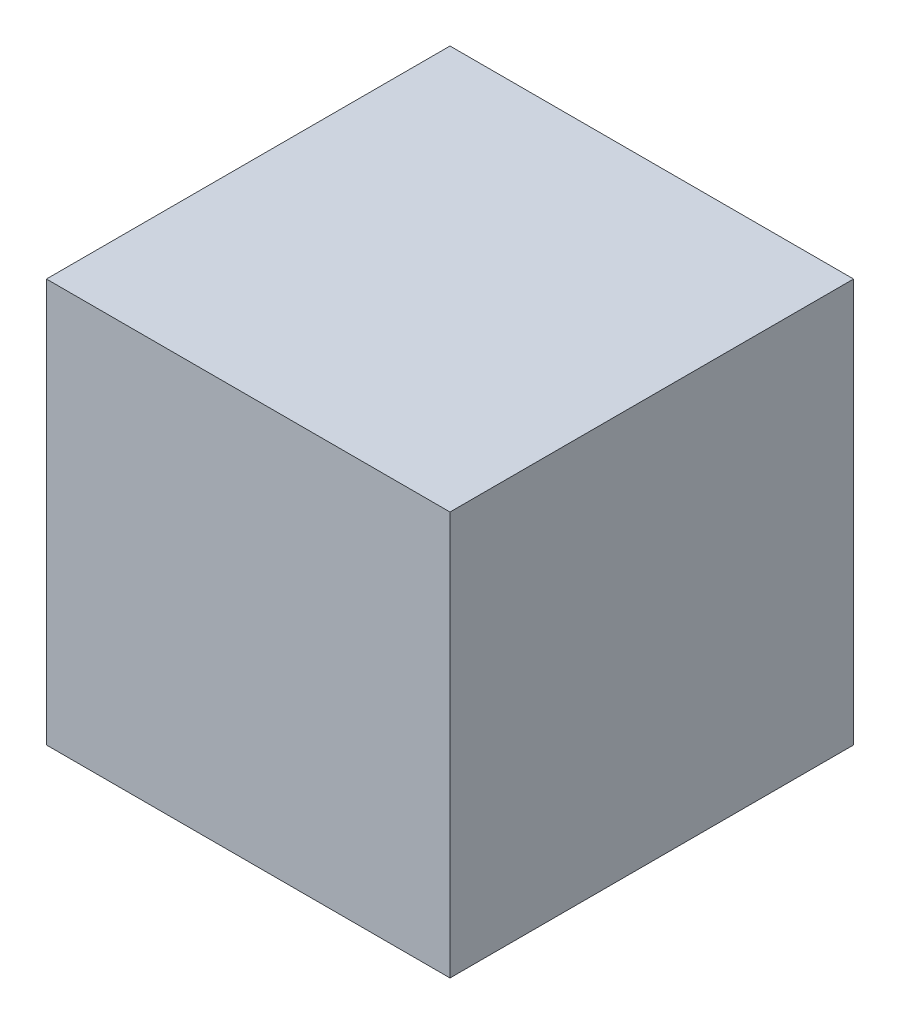
SolidWorks part; units mm, degrees
ref_plane "Front Plane" through (0, 0, 0) normal (0, 0, 1) x (1, 0, 0)
ref_plane "Top Plane" through (0, 0, 0) normal (0, 1, 0) x (1, 0, 0)
ref_plane "Right Plane" through (0, 0, 0) normal (1, 0, 0) x (0, 0, -1)
sketch "Sketch2" plane through (0, 0, 0) normal (0, 1, 0) x (1, 0, 0)
  line L1 (0, 0) -> (304.8, 0)
  line L2 (0, 0) -> (0, 304.8)
  line L3 (0, 304.8) -> (304.8, 304.8)
  line L4 (304.8, 0) -> (304.8, 304.8)
extrude "Boss-Extrude1" add sketch "Sketch2" along normal blind 304.8
